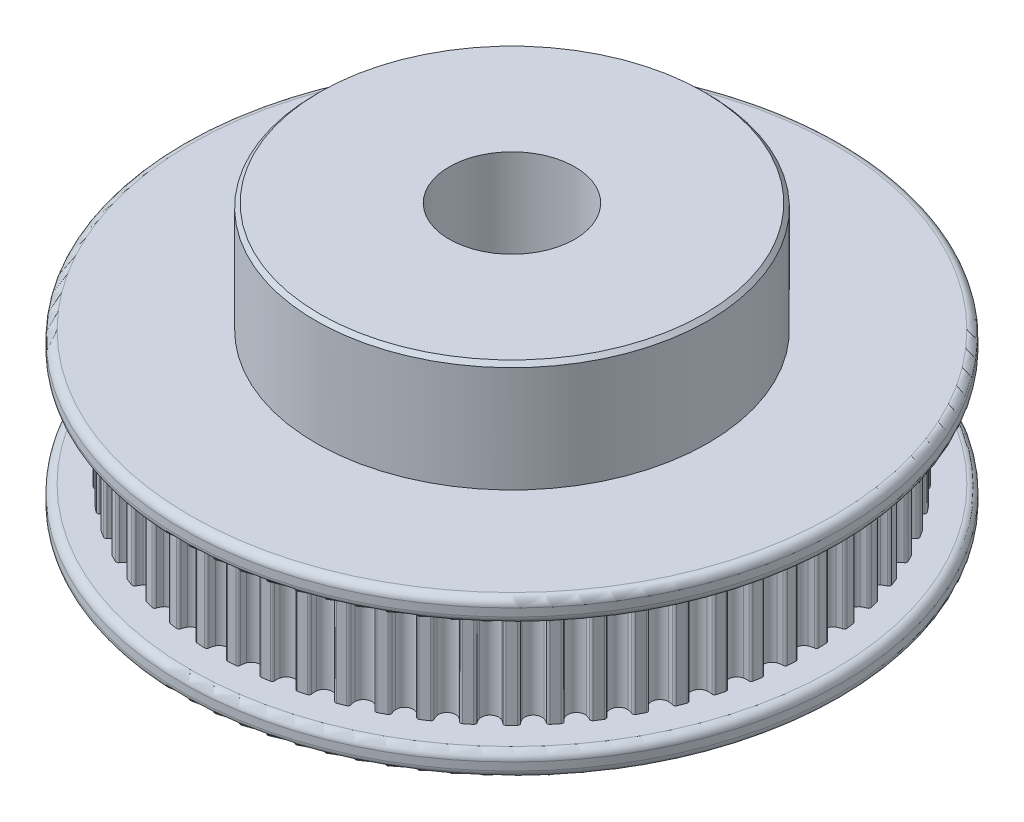
SolidWorks part; units mm, degrees
ref_plane "Front Plane" through (0, 0, 0) normal (0, 0, 1) x (1, 0, 0)
ref_plane "Top Plane" through (0, 0, 0) normal (0, 1, 0) x (1, 0, 0)
ref_plane "Right Plane" through (0, 0, 0) normal (1, 0, 0) x (0, 0, -1)
sketch "Sketch1" plane through (0, 0, 0) normal (0, 0, 1) x (1, 0, 0)
  line L0 (0, -5.5789) -> (0, 5.5789) construction
  line L3 (4, 7.1842) -> (4, 14.1842)
  line L4 (4, 14.1842) -> (12.5, 14.1842)
  line L5 (12.5, 7.1842) -> (12.5, 14.1842)
  line L6 (12.5, 7.1842) -> (21, 7.1842)
  line L7 (4, 7.1842) -> (4, -2.8158)
  line L8 (4, -2.8158) -> (21, -2.8158)
  line L9 (21, 7.1842) -> (21, -2.8158)
  point P4 (0, 0)
  dimension "D1" = 4
  dimension "D2" = 12.5
  dimension "D3" = 21
  dimension "D4" = 7
  dimension "D5" = 10
revolve "Revolve1" add sketch "Sketch1" angle 360 about L0
sketch "Sketch2" plane through (0, -2.8158, 0) normal (0, -1, 0) x (1, 0, 0)
  circle A421 centre (-0.0034, -0.0089) radius 24.4811
  circle B0 centre (0, 0) radius 4
  arc B1 (18.8305, -0.7295) -> (18.6999, -0.5808) centre (18.6805, -0.7295) ccw
  arc B2 (18.376, -0.4956) -> (18.6999, -0.5808) centre (18.7887, 0.4152) ccw
  arc B3 (18.0692, 0.0008) -> (18.376, -0.4956) centre (18.6242, 0.0008) ccw
  arc B4 (18.376, 0.4972) -> (18.0692, 0.0008) centre (18.6242, 0.0008) ccw
  arc B5 (18.6999, 0.5824) -> (18.376, 0.4972) centre (18.7887, -0.4136) ccw
  arc B6 (18.6999, 0.5824) -> (18.8305, 0.7311) centre (18.6805, 0.7311) ccw
  arc B7 (18.8305, 0.7311) -> (18.8036, 1.2444) centre (0, 0.0016) ccw
  arc B8 (18.8036, 1.2444) -> (18.6581, 1.3787) centre (18.6544, 1.2287) ccw
  arc B9 (18.3271, 1.4295) -> (18.6581, 1.3787) centre (18.6424, 2.3785) ccw
  arc B10 (17.9701, 1.8912) -> (18.3271, 1.4295) centre (18.5221, 1.9492) ccw
  arc B11 (18.2234, 2.4169) -> (17.9701, 1.8912) centre (18.5221, 1.9492) ccw
  arc B12 (18.5365, 2.5355) -> (18.2234, 2.4169) centre (18.7291, 1.5542) ccw
  arc B13 (18.5365, 2.5355) -> (18.6509, 2.6971) centre (18.5017, 2.6814) ccw
  arc B14 (18.6509, 2.6971) -> (18.5705, 3.2047) centre (-0.0002, 0.0032) ccw
  arc B15 (18.5705, 3.2047) -> (18.4118, 3.323) centre (18.4238, 3.1735) ccw
  arc B16 (18.0773, 3.339) -> (18.4118, 3.323) centre (18.2917, 4.3158) ccw
  arc B17 (17.674, 3.7608) -> (18.0773, 3.339) centre (18.2169, 3.8762) ccw
  arc B18 (17.8709, 4.3102) -> (17.674, 3.7608) centre (18.2169, 3.8762) ccw
  arc B19 (18.17, 4.4608) -> (17.8709, 4.3102) centre (18.464, 3.505) ccw
  arc B20 (18.17, 4.4608) -> (18.2668, 4.6335) centre (18.1201, 4.6023) ccw
  arc B21 (18.2668, 4.6335) -> (18.1338, 5.1299) centre (-0.0005, 0.0048) ccw
  arc B22 (18.1338, 5.1299) -> (17.9636, 5.231) centre (17.9911, 5.0835) ccw
  arc B23 (17.6293, 5.2119) -> (17.9636, 5.231) centre (17.7403, 6.2058) ccw
  arc B24 (17.1841, 5.5893) -> (17.6293, 5.2119) centre (17.7119, 5.7608) ccw
  arc B25 (17.3225, 6.1562) -> (17.1841, 5.5893) centre (17.7119, 5.7608) ccw
  arc B26 (17.6042, 6.3373) -> (17.3225, 6.1562) centre (17.9965, 5.4174) ccw
  arc B27 (17.6042, 6.3373) -> (17.6824, 6.5191) centre (17.5397, 6.4727) ccw
  arc B28 (17.6824, 6.5191) -> (17.4982, 6.9989) centre (-0.001, 0.0063) ccw
  arc B29 (17.4982, 6.9989) -> (17.3184, 7.0817) centre (17.3612, 6.9379) ccw
  arc B30 (16.9879, 7.0278) -> (17.3184, 7.0817) centre (16.9945, 8.0277) ccw
  arc B31 (16.5057, 7.3565) -> (16.9879, 7.0278) centre (17.0127, 7.5822) ccw
  arc B32 (16.5841, 7.9347) -> (16.5057, 7.3565) centre (17.0127, 7.5822) ccw
  arc B33 (16.8453, 8.1443) -> (16.5841, 7.9347) centre (17.3316, 7.2705) ccw
  arc B34 (16.8453, 8.1443) -> (16.9041, 8.3333) centre (16.7671, 8.2723) ccw
  arc B35 (16.9041, 8.3333) -> (16.6708, 8.7912) centre (-0.0017, 0.0078) ccw
  arc B36 (16.6708, 8.7912) -> (16.4833, 8.8548) centre (16.5409, 8.7162) ccw
  arc B37 (16.1602, 8.7666) -> (16.4833, 8.8548) centre (16.0622, 9.7618) ccw
  arc B38 (15.6463, 9.0431) -> (16.1602, 8.7666) centre (16.127, 9.3206) ccw
  arc B39 (15.6638, 9.6264) -> (15.6463, 9.0431) centre (16.127, 9.3206) ccw
  arc B40 (15.9017, 9.8621) -> (15.6638, 9.6264) centre (16.4767, 9.044) ccw
  arc B41 (15.9017, 9.8621) -> (15.9404, 10.0562) centre (15.8105, 9.9812) ccw
  arc B42 (15.9404, 10.0562) -> (15.6605, 10.4873) centre (-0.0025, 0.0092) ccw
  arc B43 (15.6605, 10.4873) -> (15.4674, 10.5308) centre (15.5392, 10.3991) ccw
  arc B44 (15.1553, 10.4094) -> (15.4674, 10.5308) centre (14.9539, 11.3889) ccw
  arc B45 (14.6154, 10.6307) -> (15.1553, 10.4094) centre (15.0644, 10.9569) ccw
  arc B46 (14.5718, 11.2126) -> (14.6154, 10.6307) centre (15.0644, 10.9569) ccw
  arc B47 (14.7837, 11.4719) -> (14.5718, 11.2126) centre (15.4411, 10.7183) ccw
  arc B48 (14.7837, 11.4719) -> (14.8019, 11.669) centre (14.6806, 11.5808) ccw
  arc B49 (14.8019, 11.669) -> (14.4785, 12.0684) centre (-0.0034, 0.0105) ccw
  arc B50 (14.4785, 12.0684) -> (14.2819, 12.0915) centre (14.367, 11.968) ccw
  arc B51 (13.9842, 11.9381) -> (14.2819, 12.0915) centre (13.6815, 12.8912) ccw
  arc B52 (13.4241, 12.1018) -> (13.9842, 11.9381) centre (13.8365, 12.4731) ccw
  arc B53 (13.3199, 12.676) -> (13.4241, 12.1018) centre (13.8365, 12.4731) ccw
  arc B54 (13.5036, 12.956) -> (13.3199, 12.676) centre (14.2361, 12.2752) ccw
  arc B55 (13.5036, 12.956) -> (13.5011, 13.1539) centre (13.3896, 13.0535) ccw
  arc B56 (13.5011, 13.1539) -> (13.1377, 13.5173) centre (-0.0045, 0.0117) ccw
  arc B57 (13.1377, 13.5173) -> (12.9398, 13.5198) centre (13.0373, 13.4058) ccw
  arc B58 (12.6598, 13.3361) -> (12.9398, 13.5198) centre (12.259, 14.2523) ccw
  arc B59 (12.0856, 13.4403) -> (12.6598, 13.3361) centre (12.4569, 13.8527) ccw
  arc B60 (11.922, 14.0004) -> (12.0856, 13.4403) centre (12.4569, 13.8527) ccw
  arc B61 (12.0753, 14.2981) -> (11.922, 14.0004) centre (12.875, 13.6977) ccw
  arc B62 (12.0753, 14.2981) -> (12.0522, 14.4947) centre (11.9518, 14.3832) ccw
  arc B63 (12.0522, 14.4947) -> (11.6528, 14.8181) centre (-0.0057, 0.0128) ccw
  arc B64 (11.6528, 14.8181) -> (11.4557, 14.7999) centre (11.5646, 14.6968) ccw
  arc B65 (11.1964, 14.588) -> (11.4557, 14.7999) centre (10.7021, 15.4573) ccw
  arc B66 (10.6145, 14.6315) -> (11.1964, 14.588) centre (10.9407, 15.0806) ccw
  arc B67 (10.3932, 15.1715) -> (10.6145, 14.6315) centre (10.9407, 15.0806) ccw
  arc B68 (10.5146, 15.4836) -> (10.3932, 15.1715) centre (11.3727, 14.9701) ccw
  arc B69 (10.5146, 15.4836) -> (10.4711, 15.6767) centre (10.3829, 15.5554) ccw
  arc B70 (10.4711, 15.6767) -> (10.04, 15.9566) centre (-0.007, 0.0137) ccw
  arc B71 (10.04, 15.9566) -> (9.8459, 15.9179) centre (9.965, 15.8267) ccw
  arc B72 (9.6102, 15.68) -> (9.8459, 15.9179) centre (9.0278, 16.4929) ccw
  arc B73 (9.0269, 15.6625) -> (9.6102, 15.68) centre (9.3044, 16.1432) ccw
  arc B74 (8.7504, 16.1764) -> (9.0269, 15.6625) centre (9.3044, 16.1432) ccw
  arc B75 (8.8386, 16.4995) -> (8.7504, 16.1764) centre (9.7456, 16.0784) ccw
  arc B76 (8.8386, 16.4995) -> (8.775, 16.687) centre (8.7, 16.5571) ccw
  arc B77 (8.775, 16.687) -> (8.3171, 16.9203) centre (-0.0084, 0.0145) ccw
  arc B78 (8.3171, 16.9203) -> (8.1281, 16.8615) centre (8.2561, 16.7833) ccw
  arc B79 (7.9186, 16.6003) -> (8.1281, 16.8615) centre (7.2543, 17.3478) ccw
  arc B80 (7.3403, 16.5219) -> (7.9186, 16.6003) centre (7.566, 17.0289) ccw
  arc B81 (7.0116, 17.0041) -> (7.3403, 16.5219) centre (7.566, 17.0289) ccw
  arc B82 (7.0655, 17.3346) -> (7.0116, 17.0041) centre (8.0116, 17.0107) ccw
  arc B83 (7.0655, 17.3346) -> (6.9827, 17.5144) centre (6.9217, 17.3774) ccw
  arc B84 (6.9827, 17.5144) -> (6.5029, 17.6986) centre (-0.0099, 0.0152) ccw
  arc B85 (6.5029, 17.6986) -> (6.3211, 17.6203) centre (6.4565, 17.5559) ccw
  arc B86 (6.14, 17.3387) -> (6.3211, 17.6203) centre (5.4013, 18.0127) ccw
  arc B87 (5.5731, 17.2003) -> (6.14, 17.3387) centre (5.7446, 17.7281) ccw
  arc B88 (5.1958, 17.6455) -> (5.5731, 17.2003) centre (5.7446, 17.7281) ccw
  arc B89 (5.2148, 17.9798) -> (5.1958, 17.6455) centre (6.1896, 17.7565) ccw
  arc B90 (5.2148, 17.9798) -> (5.1137, 18.15) centre (5.0674, 18.0073) ccw
  arc B91 (5.1137, 18.15) -> (4.6173, 18.283) centre (-0.0114, 0.0157) ccw
  arc B92 (4.6173, 18.283) -> (4.4446, 18.1862) centre (4.5861, 18.1363) ccw
  arc B93 (4.294, 17.8871) -> (4.4446, 18.1862) centre (3.4888, 18.4802) ccw
  arc B94 (3.7446, 17.6902) -> (4.294, 17.8871) centre (3.86, 18.2331) ccw
  arc B95 (3.3228, 18.0935) -> (3.7446, 17.6902) centre (3.86, 18.2331) ccw
  arc B96 (3.3068, 18.428) -> (3.3228, 18.0935) centre (4.2996, 18.3079) ccw
  arc B97 (3.3068, 18.428) -> (3.1885, 18.5867) centre (3.1573, 18.44) ccw
  arc B98 (3.1885, 18.5867) -> (2.6809, 18.6671) centre (-0.013, 0.016) ccw
  arc B99 (2.6809, 18.6671) -> (2.5193, 18.5527) centre (2.6652, 18.5179) ccw
  arc B100 (2.4007, 18.2396) -> (2.5193, 18.5527) centre (1.538, 18.7452) ccw
  arc B101 (1.875, 17.9863) -> (2.4007, 18.2396) centre (1.933, 18.5383) ccw
  arc B102 (1.4133, 18.3433) -> (1.875, 17.9863) centre (1.933, 18.5383) ccw
  arc B103 (1.3625, 18.6743) -> (1.4133, 18.3433) centre (2.3624, 18.6586) ccw
  arc B104 (1.3625, 18.6743) -> (1.2282, 18.8198) centre (1.2125, 18.6706) ccw
  arc B105 (1.2282, 18.8198) -> (0.715, 18.8467) centre (-0.0146, 0.0162) ccw
  arc B106 (0.715, 18.8467) -> (0.5662, 18.7161) centre (0.715, 18.6967) ccw
  arc B107 (0.481, 18.3922) -> (0.5662, 18.7161) centre (-0.4298, 18.8049) ccw
  arc B108 (-0.0154, 18.0854) -> (0.481, 18.3922) centre (-0.0154, 18.6404) ccw
  arc B109 (-0.5118, 18.3922) -> (-0.0154, 18.0854) centre (-0.0154, 18.6404) ccw
  arc B110 (-0.597, 18.7161) -> (-0.5118, 18.3922) centre (0.3991, 18.8049) ccw
  arc B111 (-0.597, 18.7161) -> (-0.7457, 18.8467) centre (-0.7457, 18.6967) ccw
  arc B112 (-0.7457, 18.8467) -> (-1.259, 18.8198) centre (-0.0162, 0.0162) ccw
  arc B113 (-1.259, 18.8198) -> (-1.3932, 18.6743) centre (-1.2433, 18.6706) ccw
  arc B114 (-1.4441, 18.3433) -> (-1.3932, 18.6743) centre (-2.3931, 18.6586) ccw
  arc B115 (-1.9057, 17.9863) -> (-1.4441, 18.3433) centre (-1.9638, 18.5383) ccw
  arc B116 (-2.4315, 18.2396) -> (-1.9057, 17.9863) centre (-1.9638, 18.5383) ccw
  arc B117 (-2.5501, 18.5527) -> (-2.4315, 18.2396) centre (-1.5688, 18.7452) ccw
  arc B118 (-2.5501, 18.5527) -> (-2.7117, 18.6671) centre (-2.696, 18.5179) ccw
  arc B119 (-2.7117, 18.6671) -> (-3.2193, 18.5867) centre (-0.0178, 0.016) ccw
  arc B120 (-3.2193, 18.5867) -> (-3.3376, 18.428) centre (-3.1881, 18.44) ccw
  arc B121 (-3.3536, 18.0935) -> (-3.3376, 18.428) centre (-4.3304, 18.3079) ccw
  arc B122 (-3.7754, 17.6902) -> (-3.3536, 18.0935) centre (-3.8908, 18.2331) ccw
  arc B123 (-4.3247, 17.8871) -> (-3.7754, 17.6902) centre (-3.8908, 18.2331) ccw
  arc B124 (-4.4754, 18.1862) -> (-4.3247, 17.8871) centre (-3.5196, 18.4802) ccw
  arc B125 (-4.4754, 18.1862) -> (-4.648, 18.283) centre (-4.6169, 18.1363) ccw
  arc B126 (-4.648, 18.283) -> (-5.1445, 18.15) centre (-0.0194, 0.0157) ccw
  arc B127 (-5.1445, 18.15) -> (-5.2456, 17.9798) centre (-5.0981, 18.0073) ccw
  arc B128 (-5.2265, 17.6455) -> (-5.2456, 17.9798) centre (-6.2203, 17.7565) ccw
  arc B129 (-5.6038, 17.2003) -> (-5.2265, 17.6455) centre (-5.7753, 17.7281) ccw
  arc B130 (-6.1707, 17.3387) -> (-5.6038, 17.2003) centre (-5.7753, 17.7281) ccw
  arc B131 (-6.3519, 17.6203) -> (-6.1707, 17.3387) centre (-5.432, 18.0127) ccw
  arc B132 (-6.3519, 17.6203) -> (-6.5337, 17.6986) centre (-6.4873, 17.5559) ccw
  arc B133 (-6.5337, 17.6986) -> (-7.0135, 17.5144) centre (-0.0209, 0.0152) ccw
  arc B134 (-7.0135, 17.5144) -> (-7.0962, 17.3346) centre (-6.9525, 17.3774) ccw
  arc B135 (-7.0423, 17.0041) -> (-7.0962, 17.3346) centre (-8.0423, 17.0107) ccw
  arc B136 (-7.3711, 16.5219) -> (-7.0423, 17.0041) centre (-7.5968, 17.0289) ccw
  arc B137 (-7.9493, 16.6003) -> (-7.3711, 16.5219) centre (-7.5968, 17.0289) ccw
  arc B138 (-8.1589, 16.8615) -> (-7.9493, 16.6003) centre (-7.2851, 17.3478) ccw
  arc B139 (-8.1589, 16.8615) -> (-8.3479, 16.9203) centre (-8.2869, 16.7833) ccw
  arc B140 (-8.3479, 16.9203) -> (-8.8058, 16.687) centre (-0.0224, 0.0145) ccw
  arc B141 (-8.8058, 16.687) -> (-8.8693, 16.4995) centre (-8.7308, 16.5571) ccw
  arc B142 (-8.7812, 16.1764) -> (-8.8693, 16.4995) centre (-9.7764, 16.0784) ccw
  arc B143 (-9.0577, 15.6625) -> (-8.7812, 16.1764) centre (-9.3352, 16.1432) ccw
  arc B144 (-9.641, 15.68) -> (-9.0577, 15.6625) centre (-9.3352, 16.1432) ccw
  arc B145 (-9.8767, 15.9179) -> (-9.641, 15.68) centre (-9.0585, 16.4929) ccw
  arc B146 (-9.8767, 15.9179) -> (-10.0708, 15.9566) centre (-9.9958, 15.8267) ccw
  arc B147 (-10.0708, 15.9566) -> (-10.5018, 15.6767) centre (-0.0238, 0.0137) ccw
  arc B148 (-10.5018, 15.6767) -> (-10.5454, 15.4836) centre (-10.4137, 15.5554) ccw
  arc B149 (-10.424, 15.1715) -> (-10.5454, 15.4836) centre (-11.4035, 14.9701) ccw
  arc B150 (-10.6452, 14.6315) -> (-10.424, 15.1715) centre (-10.9715, 15.0806) ccw
  arc B151 (-11.2272, 14.588) -> (-10.6452, 14.6315) centre (-10.9715, 15.0806) ccw
  arc B152 (-11.4865, 14.7999) -> (-11.2272, 14.588) centre (-10.7329, 15.4573) ccw
  arc B153 (-11.4865, 14.7999) -> (-11.6836, 14.8181) centre (-11.5954, 14.6968) ccw
  arc B154 (-11.6836, 14.8181) -> (-12.083, 14.4947) centre (-0.0251, 0.0128) ccw
  arc B155 (-12.083, 14.4947) -> (-12.1061, 14.2981) centre (-11.9826, 14.3832) ccw
  arc B156 (-11.9527, 14.0004) -> (-12.1061, 14.2981) centre (-12.9058, 13.6977) ccw
  arc B157 (-12.1163, 13.4403) -> (-11.9527, 14.0004) centre (-12.4877, 13.8527) ccw
  arc B158 (-12.6905, 13.3361) -> (-12.1163, 13.4403) centre (-12.4877, 13.8527) ccw
  arc B159 (-12.9705, 13.5198) -> (-12.6905, 13.3361) centre (-12.2898, 14.2523) ccw
  arc B160 (-12.9705, 13.5198) -> (-13.1685, 13.5173) centre (-13.0681, 13.4058) ccw
  arc B161 (-13.1685, 13.5173) -> (-13.5319, 13.1539) centre (-0.0263, 0.0117) ccw
  arc B162 (-13.5319, 13.1539) -> (-13.5344, 12.956) centre (-13.4204, 13.0535) ccw
  arc B163 (-13.3507, 12.676) -> (-13.5344, 12.956) centre (-14.2669, 12.2752) ccw
  arc B164 (-13.4549, 12.1018) -> (-13.3507, 12.676) centre (-13.8673, 12.4731) ccw
  arc B165 (-14.015, 11.9381) -> (-13.4549, 12.1018) centre (-13.8673, 12.4731) ccw
  arc B166 (-14.3127, 12.0915) -> (-14.015, 11.9381) centre (-13.7123, 12.8912) ccw
  arc B167 (-14.3127, 12.0915) -> (-14.5093, 12.0684) centre (-14.3978, 11.968) ccw
  arc B168 (-14.5093, 12.0684) -> (-14.8327, 11.669) centre (-0.0274, 0.0105) ccw
  arc B169 (-14.8327, 11.669) -> (-14.8145, 11.4719) centre (-14.7114, 11.5808) ccw
  arc B170 (-14.6026, 11.2126) -> (-14.8145, 11.4719) centre (-15.4718, 10.7183) ccw
  arc B171 (-14.6461, 10.6307) -> (-14.6026, 11.2126) centre (-15.0951, 10.9569) ccw
  arc B172 (-15.1861, 10.4094) -> (-14.6461, 10.6307) centre (-15.0951, 10.9569) ccw
  arc B173 (-15.4982, 10.5308) -> (-15.1861, 10.4094) centre (-14.9846, 11.3889) ccw
  arc B174 (-15.4982, 10.5308) -> (-15.6913, 10.4873) centre (-15.5699, 10.3991) ccw
  arc B175 (-15.6913, 10.4873) -> (-15.9712, 10.0562) centre (-0.0283, 0.0092) ccw
  arc B176 (-15.9712, 10.0562) -> (-15.9325, 9.8621) centre (-15.8413, 9.9812) ccw
  arc B177 (-15.6946, 9.6264) -> (-15.9325, 9.8621) centre (-16.5075, 9.044) ccw
  arc B178 (-15.6771, 9.0431) -> (-15.6946, 9.6264) centre (-16.1577, 9.3206) ccw
  arc B179 (-16.191, 8.7666) -> (-15.6771, 9.0431) centre (-16.1577, 9.3206) ccw
  arc B180 (-16.5141, 8.8548) -> (-16.191, 8.7666) centre (-16.093, 9.7618) ccw
  arc B181 (-16.5141, 8.8548) -> (-16.7015, 8.7912) centre (-16.5716, 8.7162) ccw
  arc B182 (-16.7015, 8.7912) -> (-16.9349, 8.3333) centre (-0.0291, 0.0078) ccw
  arc B183 (-16.9349, 8.3333) -> (-16.8761, 8.1443) centre (-16.7978, 8.2723) ccw
  arc B184 (-16.6149, 7.9347) -> (-16.8761, 8.1443) centre (-17.3624, 7.2705) ccw
  arc B185 (-16.5365, 7.3565) -> (-16.6149, 7.9347) centre (-17.0435, 7.5822) ccw
  arc B186 (-17.0187, 7.0278) -> (-16.5365, 7.3565) centre (-17.0435, 7.5822) ccw
  arc B187 (-17.3492, 7.0817) -> (-17.0187, 7.0278) centre (-17.0252, 8.0277) ccw
  arc B188 (-17.3492, 7.0817) -> (-17.529, 6.9989) centre (-17.392, 6.9379) ccw
  arc B189 (-17.529, 6.9989) -> (-17.7132, 6.5191) centre (-0.0298, 0.0063) ccw
  arc B190 (-17.7132, 6.5191) -> (-17.6349, 6.3373) centre (-17.5705, 6.4727) ccw
  arc B191 (-17.3532, 6.1562) -> (-17.6349, 6.3373) centre (-18.0272, 5.4174) ccw
  arc B192 (-17.2149, 5.5893) -> (-17.3532, 6.1562) centre (-17.7427, 5.7608) ccw
  arc B193 (-17.66, 5.2119) -> (-17.2149, 5.5893) centre (-17.7427, 5.7608) ccw
  arc B194 (-17.9944, 5.231) -> (-17.66, 5.2119) centre (-17.7711, 6.2058) ccw
  arc B195 (-17.9944, 5.231) -> (-18.1645, 5.1299) centre (-18.0219, 5.0835) ccw
  arc B196 (-18.1645, 5.1299) -> (-18.2976, 4.6335) centre (-0.0303, 0.0048) ccw
  arc B197 (-18.2976, 4.6335) -> (-18.2007, 4.4608) centre (-18.1508, 4.6023) ccw
  arc B198 (-17.9017, 4.3102) -> (-18.2007, 4.4608) centre (-18.4948, 3.505) ccw
  arc B199 (-17.7048, 3.7608) -> (-17.9017, 4.3102) centre (-18.2477, 3.8762) ccw
  arc B200 (-18.1081, 3.339) -> (-17.7048, 3.7608) centre (-18.2477, 3.8762) ccw
  arc B201 (-18.4426, 3.323) -> (-18.1081, 3.339) centre (-18.3224, 4.3158) ccw
  arc B202 (-18.4426, 3.323) -> (-18.6013, 3.2047) centre (-18.4545, 3.1735) ccw
  arc B203 (-18.6013, 3.2047) -> (-18.6817, 2.6971) centre (-0.0306, 0.0032) ccw
  arc B204 (-18.6817, 2.6971) -> (-18.5673, 2.5355) centre (-18.5325, 2.6814) ccw
  arc B205 (-18.2541, 2.4169) -> (-18.5673, 2.5355) centre (-18.7598, 1.5542) ccw
  arc B206 (-18.0009, 1.8912) -> (-18.2541, 2.4169) centre (-18.5529, 1.9492) ccw
  arc B207 (-18.3579, 1.4295) -> (-18.0009, 1.8912) centre (-18.5529, 1.9492) ccw
  arc B208 (-18.6889, 1.3787) -> (-18.3579, 1.4295) centre (-18.6732, 2.3785) ccw
  arc B209 (-18.6889, 1.3787) -> (-18.8343, 1.2444) centre (-18.6852, 1.2287) ccw
  arc B210 (-18.8343, 1.2444) -> (-18.8612, 0.7311) centre (-0.0308, 0.0016) ccw
  arc B211 (-18.8612, 0.7311) -> (-18.7306, 0.5824) centre (-18.7112, 0.7311) ccw
  arc B212 (-18.4068, 0.4972) -> (-18.7306, 0.5824) centre (-18.8195, -0.4136) ccw
  arc B213 (-18.1, 0.0008) -> (-18.4068, 0.4972) centre (-18.655, 0.0008) ccw
  arc B214 (-18.4068, -0.4956) -> (-18.1, 0.0008) centre (-18.655, 0.0008) ccw
  arc B215 (-18.7306, -0.5808) -> (-18.4068, -0.4956) centre (-18.8195, 0.4152) ccw
  arc B216 (-18.7306, -0.5808) -> (-18.8612, -0.7295) centre (-18.7112, -0.7295) ccw
  arc B217 (-18.8612, -0.7295) -> (-18.8343, -1.2428) centre (-0.0308, 0) ccw
  arc B218 (-18.8343, -1.2428) -> (-18.6889, -1.3771) centre (-18.6852, -1.2271) ccw
  arc B219 (-18.3579, -1.4279) -> (-18.6889, -1.3771) centre (-18.6732, -2.3769) ccw
  arc B220 (-18.0009, -1.8895) -> (-18.3579, -1.4279) centre (-18.5529, -1.9476) ccw
  arc B221 (-18.2541, -2.4153) -> (-18.0009, -1.8895) centre (-18.5529, -1.9476) ccw
  arc B222 (-18.5673, -2.5339) -> (-18.2541, -2.4153) centre (-18.7598, -1.5526) ccw
  arc B223 (-18.5673, -2.5339) -> (-18.6817, -2.6955) centre (-18.5325, -2.6798) ccw
  arc B224 (-18.6817, -2.6955) -> (-18.6013, -3.2031) centre (-0.0306, -0.0016) ccw
  arc B225 (-18.6013, -3.2031) -> (-18.4426, -3.3214) centre (-18.4545, -3.1719) ccw
  arc B226 (-18.1081, -3.3374) -> (-18.4426, -3.3214) centre (-18.3224, -4.3142) ccw
  arc B227 (-17.7048, -3.7592) -> (-18.1081, -3.3374) centre (-18.2477, -3.8746) ccw
  arc B228 (-17.9017, -4.3085) -> (-17.7048, -3.7592) centre (-18.2477, -3.8746) ccw
  arc B229 (-18.2007, -4.4592) -> (-17.9017, -4.3085) centre (-18.4948, -3.5034) ccw
  arc B230 (-18.2007, -4.4592) -> (-18.2976, -4.6318) centre (-18.1508, -4.6007) ccw
  arc B231 (-18.2976, -4.6318) -> (-18.1645, -5.1283) centre (-0.0303, -0.0032) ccw
  arc B232 (-18.1645, -5.1283) -> (-17.9944, -5.2294) centre (-18.0219, -5.0819) ccw
  arc B233 (-17.66, -5.2103) -> (-17.9944, -5.2294) centre (-17.7711, -6.2041) ccw
  arc B234 (-17.2149, -5.5876) -> (-17.66, -5.2103) centre (-17.7427, -5.7591) ccw
  arc B235 (-17.3532, -6.1546) -> (-17.2149, -5.5876) centre (-17.7427, -5.7591) ccw
  arc B236 (-17.6349, -6.3357) -> (-17.3532, -6.1546) centre (-18.0272, -5.4158) ccw
  arc B237 (-17.6349, -6.3357) -> (-17.7132, -6.5175) centre (-17.5705, -6.4711) ccw
  arc B238 (-17.7132, -6.5175) -> (-17.529, -6.9973) centre (-0.0298, -0.0047) ccw
  arc B239 (-17.529, -6.9973) -> (-17.3492, -7.0801) centre (-17.392, -6.9363) ccw
  arc B240 (-17.0187, -7.0262) -> (-17.3492, -7.0801) centre (-17.0252, -8.0261) ccw
  arc B241 (-16.5365, -7.3549) -> (-17.0187, -7.0262) centre (-17.0435, -7.5806) ccw
  arc B242 (-16.6149, -7.9331) -> (-16.5365, -7.3549) centre (-17.0435, -7.5806) ccw
  arc B243 (-16.8761, -8.1427) -> (-16.6149, -7.9331) centre (-17.3624, -7.2689) ccw
  arc B244 (-16.8761, -8.1427) -> (-16.9349, -8.3317) centre (-16.7978, -8.2707) ccw
  arc B245 (-16.9349, -8.3317) -> (-16.7015, -8.7896) centre (-0.0291, -0.0062) ccw
  arc B246 (-16.7015, -8.7896) -> (-16.5141, -8.8531) centre (-16.5716, -8.7146) ccw
  arc B247 (-16.191, -8.765) -> (-16.5141, -8.8531) centre (-16.093, -9.7602) ccw
  arc B248 (-15.6771, -9.0415) -> (-16.191, -8.765) centre (-16.1577, -9.319) ccw
  arc B249 (-15.6946, -9.6248) -> (-15.6771, -9.0415) centre (-16.1577, -9.319) ccw
  arc B250 (-15.9325, -9.8605) -> (-15.6946, -9.6248) centre (-16.5075, -9.0423) ccw
  arc B251 (-15.9325, -9.8605) -> (-15.9712, -10.0546) centre (-15.8413, -9.9796) ccw
  arc B252 (-15.9712, -10.0546) -> (-15.6913, -10.4857) centre (-0.0283, -0.0076) ccw
  arc B253 (-15.6913, -10.4857) -> (-15.4982, -10.5292) centre (-15.5699, -10.3975) ccw
  arc B254 (-15.1861, -10.4078) -> (-15.4982, -10.5292) centre (-14.9846, -11.3873) ccw
  arc B255 (-14.6461, -10.6291) -> (-15.1861, -10.4078) centre (-15.0951, -10.9553) ccw
  arc B256 (-14.6026, -11.211) -> (-14.6461, -10.6291) centre (-15.0951, -10.9553) ccw
  arc B257 (-14.8145, -11.4703) -> (-14.6026, -11.211) centre (-15.4718, -10.7167) ccw
  arc B258 (-14.8145, -11.4703) -> (-14.8327, -11.6674) centre (-14.7114, -11.5792) ccw
  arc B259 (-14.8327, -11.6674) -> (-14.5093, -12.0668) centre (-0.0274, -0.0089) ccw
  arc B260 (-14.5093, -12.0668) -> (-14.3127, -12.0899) centre (-14.3978, -11.9664) ccw
  arc B261 (-14.015, -11.9365) -> (-14.3127, -12.0899) centre (-13.7123, -12.8896) ccw
  arc B262 (-13.4549, -12.1001) -> (-14.015, -11.9365) centre (-13.8673, -12.4715) ccw
  arc B263 (-13.3507, -12.6743) -> (-13.4549, -12.1001) centre (-13.8673, -12.4715) ccw
  arc B264 (-13.5344, -12.9544) -> (-13.3507, -12.6743) centre (-14.2669, -12.2736) ccw
  arc B265 (-13.5344, -12.9544) -> (-13.5319, -13.1523) centre (-13.4204, -13.0519) ccw
  arc B266 (-13.5319, -13.1523) -> (-13.1685, -13.5157) centre (-0.0263, -0.0101) ccw
  arc B267 (-13.1685, -13.5157) -> (-12.9705, -13.5182) centre (-13.0681, -13.4042) ccw
  arc B268 (-12.6905, -13.3345) -> (-12.9705, -13.5182) centre (-12.2898, -14.2507) ccw
  arc B269 (-12.1163, -13.4387) -> (-12.6905, -13.3345) centre (-12.4877, -13.8511) ccw
  arc B270 (-11.9527, -13.9988) -> (-12.1163, -13.4387) centre (-12.4877, -13.8511) ccw
  arc B271 (-12.1061, -14.2965) -> (-11.9527, -13.9988) centre (-12.9058, -13.6961) ccw
  arc B272 (-12.1061, -14.2965) -> (-12.083, -14.4931) centre (-11.9826, -14.3816) ccw
  arc B273 (-12.083, -14.4931) -> (-11.6836, -14.8165) centre (-0.0251, -0.0112) ccw
  arc B274 (-11.6836, -14.8165) -> (-11.4865, -14.7983) centre (-11.5954, -14.6952) ccw
  arc B275 (-11.2272, -14.5864) -> (-11.4865, -14.7983) centre (-10.7329, -15.4557) ccw
  arc B276 (-10.6452, -14.6299) -> (-11.2272, -14.5864) centre (-10.9715, -15.0789) ccw
  arc B277 (-10.424, -15.1699) -> (-10.6452, -14.6299) centre (-10.9715, -15.0789) ccw
  arc B278 (-10.5454, -15.482) -> (-10.424, -15.1699) centre (-11.4035, -14.9684) ccw
  arc B279 (-10.5454, -15.482) -> (-10.5018, -15.6751) centre (-10.4137, -15.5537) ccw
  arc B280 (-10.5018, -15.6751) -> (-10.0708, -15.955) centre (-0.0238, -0.0121) ccw
  arc B281 (-10.0708, -15.955) -> (-9.8767, -15.9163) centre (-9.9958, -15.8251) ccw
  arc B282 (-9.641, -15.6784) -> (-9.8767, -15.9163) centre (-9.0585, -16.4913) ccw
  arc B283 (-9.0577, -15.6609) -> (-9.641, -15.6784) centre (-9.3352, -16.1416) ccw
  arc B284 (-8.7812, -16.1748) -> (-9.0577, -15.6609) centre (-9.3352, -16.1416) ccw
  arc B285 (-8.8693, -16.4979) -> (-8.7812, -16.1748) centre (-9.7764, -16.0768) ccw
  arc B286 (-8.8693, -16.4979) -> (-8.8058, -16.6854) centre (-8.7308, -16.5554) ccw
  arc B287 (-8.8058, -16.6854) -> (-8.3479, -16.9187) centre (-0.0224, -0.0129) ccw
  arc B288 (-8.3479, -16.9187) -> (-8.1589, -16.8599) centre (-8.2869, -16.7816) ccw
  arc B289 (-7.9493, -16.5987) -> (-8.1589, -16.8599) centre (-7.2851, -17.3462) ccw
  arc B290 (-7.3711, -16.5203) -> (-7.9493, -16.5987) centre (-7.5968, -17.0273) ccw
  arc B291 (-7.0423, -17.0025) -> (-7.3711, -16.5203) centre (-7.5968, -17.0273) ccw
  arc B292 (-7.0962, -17.333) -> (-7.0423, -17.0025) centre (-8.0423, -17.0091) ccw
  arc B293 (-7.0962, -17.333) -> (-7.0135, -17.5128) centre (-6.9525, -17.3758) ccw
  arc B294 (-7.0135, -17.5128) -> (-6.5337, -17.697) centre (-0.0209, -0.0136) ccw
  arc B295 (-6.5337, -17.697) -> (-6.3519, -17.6187) centre (-6.4873, -17.5543) ccw
  arc B296 (-6.1707, -17.337) -> (-6.3519, -17.6187) centre (-5.432, -18.0111) ccw
  arc B297 (-5.6038, -17.1987) -> (-6.1707, -17.337) centre (-5.7753, -17.7265) ccw
  arc B298 (-5.2265, -17.6438) -> (-5.6038, -17.1987) centre (-5.7753, -17.7265) ccw
  arc B299 (-5.2456, -17.9782) -> (-5.2265, -17.6438) centre (-6.2203, -17.7549) ccw
  arc B300 (-5.2456, -17.9782) -> (-5.1445, -18.1484) centre (-5.0981, -18.0057) ccw
  arc B301 (-5.1445, -18.1484) -> (-4.648, -18.2814) centre (-0.0194, -0.0141) ccw
  arc B302 (-4.648, -18.2814) -> (-4.4754, -18.1846) centre (-4.6169, -18.1347) ccw
  arc B303 (-4.3247, -17.8855) -> (-4.4754, -18.1846) centre (-3.5196, -18.4786) ccw
  arc B304 (-3.7754, -17.6886) -> (-4.3247, -17.8855) centre (-3.8908, -18.2315) ccw
  arc B305 (-3.3536, -18.0919) -> (-3.7754, -17.6886) centre (-3.8908, -18.2315) ccw
  arc B306 (-3.3376, -18.4264) -> (-3.3536, -18.0919) centre (-4.3304, -18.3062) ccw
  arc B307 (-3.3376, -18.4264) -> (-3.2193, -18.5851) centre (-3.1881, -18.4383) ccw
  arc B308 (-3.2193, -18.5851) -> (-2.7117, -18.6655) centre (-0.0178, -0.0144) ccw
  arc B309 (-2.7117, -18.6655) -> (-2.5501, -18.5511) centre (-2.696, -18.5163) ccw
  arc B310 (-2.4315, -18.2379) -> (-2.5501, -18.5511) centre (-1.5688, -18.7436) ccw
  arc B311 (-1.9057, -17.9847) -> (-2.4315, -18.2379) centre (-1.9638, -18.5367) ccw
  arc B312 (-1.4441, -18.3417) -> (-1.9057, -17.9847) centre (-1.9638, -18.5367) ccw
  arc B313 (-1.3932, -18.6727) -> (-1.4441, -18.3417) centre (-2.3931, -18.657) ccw
  arc B314 (-1.3932, -18.6727) -> (-1.259, -18.8181) centre (-1.2433, -18.669) ccw
  arc B315 (-1.259, -18.8181) -> (-0.7457, -18.845) centre (-0.0162, -0.0146) ccw
  arc B316 (-0.7457, -18.845) -> (-0.597, -18.7144) centre (-0.7457, -18.695) ccw
  arc B317 (-0.5118, -18.3906) -> (-0.597, -18.7144) centre (0.3991, -18.8033) ccw
  arc B318 (-0.0154, -18.0838) -> (-0.5118, -18.3906) centre (-0.0154, -18.6388) ccw
  arc B319 (0.481, -18.3906) -> (-0.0154, -18.0838) centre (-0.0154, -18.6388) ccw
  arc B320 (0.5662, -18.7144) -> (0.481, -18.3906) centre (-0.4298, -18.8033) ccw
  arc B321 (0.5662, -18.7144) -> (0.715, -18.845) centre (0.715, -18.695) ccw
  arc B322 (0.715, -18.845) -> (1.2282, -18.8181) centre (-0.0146, -0.0146) ccw
  arc B323 (1.2282, -18.8181) -> (1.3625, -18.6727) centre (1.2125, -18.669) ccw
  arc B324 (1.4133, -18.3417) -> (1.3625, -18.6727) centre (2.3624, -18.657) ccw
  arc B325 (1.875, -17.9847) -> (1.4133, -18.3417) centre (1.933, -18.5367) ccw
  arc B326 (2.4007, -18.2379) -> (1.875, -17.9847) centre (1.933, -18.5367) ccw
  arc B327 (2.5193, -18.5511) -> (2.4007, -18.2379) centre (1.538, -18.7436) ccw
  arc B328 (2.5193, -18.5511) -> (2.6809, -18.6655) centre (2.6652, -18.5163) ccw
  arc B329 (2.6809, -18.6655) -> (3.1885, -18.5851) centre (-0.013, -0.0144) ccw
  arc B330 (3.1885, -18.5851) -> (3.3068, -18.4264) centre (3.1573, -18.4383) ccw
  arc B331 (3.3228, -18.0919) -> (3.3068, -18.4264) centre (4.2996, -18.3062) ccw
  arc B332 (3.7446, -17.6886) -> (3.3228, -18.0919) centre (3.86, -18.2315) ccw
  arc B333 (4.294, -17.8855) -> (3.7446, -17.6886) centre (3.86, -18.2315) ccw
  arc B334 (4.4446, -18.1846) -> (4.294, -17.8855) centre (3.4888, -18.4786) ccw
  arc B335 (4.4446, -18.1846) -> (4.6173, -18.2814) centre (4.5861, -18.1347) ccw
  arc B336 (4.6173, -18.2814) -> (5.1137, -18.1484) centre (-0.0114, -0.0141) ccw
  arc B337 (5.1137, -18.1484) -> (5.2148, -17.9782) centre (5.0674, -18.0057) ccw
  arc B338 (5.1958, -17.6438) -> (5.2148, -17.9782) centre (6.1896, -17.7549) ccw
  arc B339 (5.5731, -17.1987) -> (5.1958, -17.6438) centre (5.7446, -17.7265) ccw
  arc B340 (6.14, -17.337) -> (5.5731, -17.1987) centre (5.7446, -17.7265) ccw
  arc B341 (6.3211, -17.6187) -> (6.14, -17.337) centre (5.4013, -18.0111) ccw
  arc B342 (6.3211, -17.6187) -> (6.5029, -17.697) centre (6.4565, -17.5543) ccw
  arc B343 (6.5029, -17.697) -> (6.9827, -17.5128) centre (-0.0099, -0.0136) ccw
  arc B344 (6.9827, -17.5128) -> (7.0655, -17.333) centre (6.9217, -17.3758) ccw
  arc B345 (7.0116, -17.0025) -> (7.0655, -17.333) centre (8.0116, -17.0091) ccw
  arc B346 (7.3403, -16.5203) -> (7.0116, -17.0025) centre (7.566, -17.0273) ccw
  arc B347 (7.9186, -16.5987) -> (7.3403, -16.5203) centre (7.566, -17.0273) ccw
  arc B348 (8.1281, -16.8599) -> (7.9186, -16.5987) centre (7.2543, -17.3462) ccw
  arc B349 (8.1281, -16.8599) -> (8.3171, -16.9187) centre (8.2561, -16.7816) ccw
  arc B350 (8.3171, -16.9187) -> (8.775, -16.6854) centre (-0.0084, -0.0129) ccw
  arc B351 (8.775, -16.6854) -> (8.8386, -16.4979) centre (8.7, -16.5554) ccw
  arc B352 (8.7504, -16.1748) -> (8.8386, -16.4979) centre (9.7456, -16.0768) ccw
  arc B353 (9.0269, -15.6609) -> (8.7504, -16.1748) centre (9.3044, -16.1416) ccw
  arc B354 (9.6102, -15.6784) -> (9.0269, -15.6609) centre (9.3044, -16.1416) ccw
  arc B355 (9.8459, -15.9163) -> (9.6102, -15.6784) centre (9.0278, -16.4913) ccw
  arc B356 (9.8459, -15.9163) -> (10.04, -15.955) centre (9.965, -15.8251) ccw
  arc B357 (10.04, -15.955) -> (10.4711, -15.6751) centre (-0.007, -0.0121) ccw
  arc B358 (10.4711, -15.6751) -> (10.5146, -15.482) centre (10.3829, -15.5537) ccw
  arc B359 (10.3932, -15.1699) -> (10.5146, -15.482) centre (11.3727, -14.9684) ccw
  arc B360 (10.6145, -14.6299) -> (10.3932, -15.1699) centre (10.9407, -15.0789) ccw
  arc B361 (11.1964, -14.5864) -> (10.6145, -14.6299) centre (10.9407, -15.0789) ccw
  arc B362 (11.4557, -14.7983) -> (11.1964, -14.5864) centre (10.7021, -15.4557) ccw
  arc B363 (11.4557, -14.7983) -> (11.6528, -14.8165) centre (11.5646, -14.6952) ccw
  arc B364 (11.6528, -14.8165) -> (12.0522, -14.4931) centre (-0.0057, -0.0112) ccw
  arc B365 (12.0522, -14.4931) -> (12.0753, -14.2965) centre (11.9518, -14.3816) ccw
  arc B366 (11.922, -13.9988) -> (12.0753, -14.2965) centre (12.875, -13.6961) ccw
  arc B367 (12.0856, -13.4387) -> (11.922, -13.9988) centre (12.4569, -13.8511) ccw
  arc B368 (12.6598, -13.3345) -> (12.0856, -13.4387) centre (12.4569, -13.8511) ccw
  arc B369 (12.9398, -13.5182) -> (12.6598, -13.3345) centre (12.259, -14.2507) ccw
  arc B370 (12.9398, -13.5182) -> (13.1377, -13.5157) centre (13.0373, -13.4042) ccw
  arc B371 (13.1377, -13.5157) -> (13.5011, -13.1523) centre (-0.0045, -0.0101) ccw
  arc B372 (13.5011, -13.1523) -> (13.5036, -12.9544) centre (13.3896, -13.0519) ccw
  arc B373 (13.3199, -12.6743) -> (13.5036, -12.9544) centre (14.2361, -12.2736) ccw
  arc B374 (13.4241, -12.1001) -> (13.3199, -12.6743) centre (13.8365, -12.4715) ccw
  arc B375 (13.9842, -11.9365) -> (13.4241, -12.1001) centre (13.8365, -12.4715) ccw
  arc B376 (14.2819, -12.0899) -> (13.9842, -11.9365) centre (13.6815, -12.8896) ccw
  arc B377 (14.2819, -12.0899) -> (14.4785, -12.0668) centre (14.367, -11.9664) ccw
  arc B378 (14.4785, -12.0668) -> (14.8019, -11.6674) centre (-0.0034, -0.0089) ccw
  arc B379 (14.8019, -11.6674) -> (14.7837, -11.4703) centre (14.6806, -11.5792) ccw
  arc B380 (14.5718, -11.211) -> (14.7837, -11.4703) centre (15.4411, -10.7167) ccw
  arc B381 (14.6154, -10.6291) -> (14.5718, -11.211) centre (15.0644, -10.9553) ccw
  arc B382 (15.1553, -10.4078) -> (14.6154, -10.6291) centre (15.0644, -10.9553) ccw
  arc B383 (15.4674, -10.5292) -> (15.1553, -10.4078) centre (14.9539, -11.3873) ccw
  arc B384 (15.4674, -10.5292) -> (15.6605, -10.4857) centre (15.5392, -10.3975) ccw
  arc B385 (15.6605, -10.4857) -> (15.9404, -10.0546) centre (-0.0025, -0.0076) ccw
  arc B386 (15.9404, -10.0546) -> (15.9017, -9.8605) centre (15.8105, -9.9796) ccw
  arc B387 (15.6638, -9.6248) -> (15.9017, -9.8605) centre (16.4767, -9.0423) ccw
  arc B388 (15.6463, -9.0415) -> (15.6638, -9.6248) centre (16.127, -9.319) ccw
  arc B389 (16.1602, -8.765) -> (15.6463, -9.0415) centre (16.127, -9.319) ccw
  arc B390 (16.4833, -8.8531) -> (16.1602, -8.765) centre (16.0622, -9.7602) ccw
  arc B391 (16.4833, -8.8531) -> (16.6708, -8.7896) centre (16.5409, -8.7146) ccw
  arc B392 (16.6708, -8.7896) -> (16.9041, -8.3317) centre (-0.0017, -0.0062) ccw
  arc B393 (16.9041, -8.3317) -> (16.8453, -8.1427) centre (16.7671, -8.2707) ccw
  arc B394 (16.5841, -7.9331) -> (16.8453, -8.1427) centre (17.3316, -7.2689) ccw
  arc B395 (16.5057, -7.3549) -> (16.5841, -7.9331) centre (17.0127, -7.5806) ccw
  arc B396 (16.9879, -7.0262) -> (16.5057, -7.3549) centre (17.0127, -7.5806) ccw
  arc B397 (17.3184, -7.0801) -> (16.9879, -7.0262) centre (16.9945, -8.0261) ccw
  arc B398 (17.3184, -7.0801) -> (17.4982, -6.9973) centre (17.3612, -6.9363) ccw
  arc B399 (17.4982, -6.9973) -> (17.6824, -6.5175) centre (-0.001, -0.0047) ccw
  arc B400 (17.6824, -6.5175) -> (17.6042, -6.3357) centre (17.5397, -6.4711) ccw
  arc B401 (17.3225, -6.1546) -> (17.6042, -6.3357) centre (17.9965, -5.4158) ccw
  arc B402 (17.1841, -5.5876) -> (17.3225, -6.1546) centre (17.7119, -5.7591) ccw
  arc B403 (17.6293, -5.2103) -> (17.1841, -5.5876) centre (17.7119, -5.7591) ccw
  arc B404 (17.9636, -5.2294) -> (17.6293, -5.2103) centre (17.7403, -6.2041) ccw
  arc B405 (17.9636, -5.2294) -> (18.1338, -5.1283) centre (17.9911, -5.0819) ccw
  arc B406 (18.1338, -5.1283) -> (18.2668, -4.6318) centre (-0.0005, -0.0032) ccw
  arc B407 (18.2668, -4.6318) -> (18.17, -4.4592) centre (18.1201, -4.6007) ccw
  arc B408 (17.8709, -4.3085) -> (18.17, -4.4592) centre (18.464, -3.5034) ccw
  arc B409 (17.674, -3.7592) -> (17.8709, -4.3085) centre (18.2169, -3.8746) ccw
  arc B410 (18.0773, -3.3374) -> (17.674, -3.7592) centre (18.2169, -3.8746) ccw
  arc B411 (18.4118, -3.3214) -> (18.0773, -3.3374) centre (18.2917, -4.3142) ccw
  arc B412 (18.4118, -3.3214) -> (18.5705, -3.2031) centre (18.4238, -3.1719) ccw
  arc B413 (18.5705, -3.2031) -> (18.6509, -2.6955) centre (-0.0002, -0.0016) ccw
  arc B414 (18.6509, -2.6955) -> (18.5365, -2.5339) centre (18.5017, -2.6798) ccw
  arc B415 (18.2234, -2.4153) -> (18.5365, -2.5339) centre (18.7291, -1.5526) ccw
  arc B416 (17.9701, -1.8895) -> (18.2234, -2.4153) centre (18.5221, -1.9476) ccw
  arc B417 (18.3271, -1.4279) -> (17.9701, -1.8895) centre (18.5221, -1.9476) ccw
  arc B418 (18.6581, -1.3771) -> (18.3271, -1.4279) centre (18.6424, -2.3769) ccw
  arc B419 (18.6581, -1.3771) -> (18.8036, -1.2428) centre (18.6544, -1.2271) ccw
  arc B420 (18.8036, -1.2428) -> (18.8305, -0.7295) centre (0, 0) ccw
  circle M1 centre (0, 0) radius 21
sketch_block_instance "Block-2gt-60-3"
sketch_block "Block-2gt-60" parameters "D1"=8
extrude "Cut-Extrude1" cut sketch "Sketch2" against normal blind 7 from offset 1.5 contours A421 M1 | B420 B419 B418 B417 B416 B415 B414 B413 B412 B411 B410 B409 B408 B407 B406 B405 B404 B403 B402 B401 B400 B399 B398 B397 B396 B395 B394 B393 B392 B391 B390 B389 B388 B387 B386 B385 B384 B383 B382 B381 B380 B379 B378 B377 B376 B375 B374 B373 B372 M1 offset against normal yes
fillet "Fillet1" radius 0.5 4 edges at (21, -2.8158, 0) (21, -1.3158, 0) (21, 5.6842, 0) (21, 7.1842, 0)
chamfer "Chamfer1" distance 0.25 angle 45 1 edges at (12.5, 14.1842, 0)
ref_plane "BeltPlane" through (0, 2.1842, 0) normal (0, 1, 0) x (1, 0, 0)
